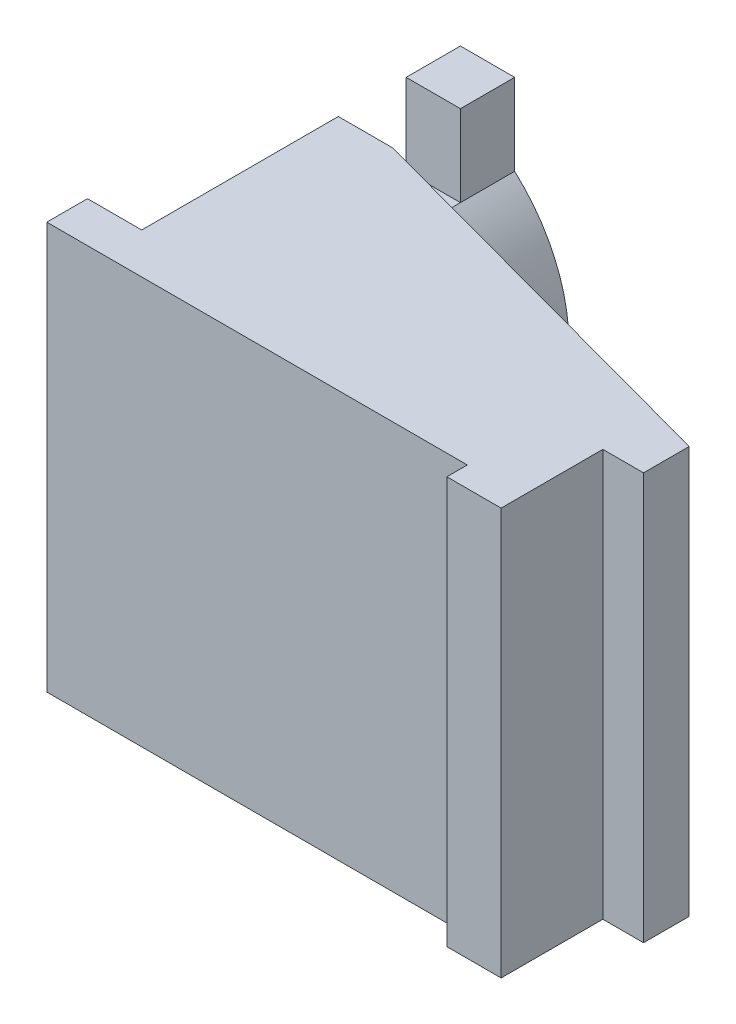
SolidWorks part; units mm, degrees
ref_plane "Front Plane" through (0, 0, 0) normal (0, 0, 1) x (1, 0, 0)
ref_plane "Top Plane" through (0, 0, 0) normal (0, 1, 0) x (1, 0, 0)
ref_plane "Right Plane" through (0, 0, 0) normal (1, 0, 0) x (0, 0, -1)
sketch "Sketch1" plane through (0, 0, 0) normal (0, 1, 0) x (1, 0, 0)
  line L4 (2, 1.5) -> (2, 13.2456)
  line L5 (2, 13.2456) -> (4, 13.2456)
  line L6 (4, 13.2456) -> (4, 8.7456)
  line L8 (17.5, -0.7544) -> (17.5, 1.1282)
  line L10 (17.5, -0.7544) -> (15.5, -0.7544)
  line L15 (17.5, 2.9956) -> (17.5, 1.1282)
  line L16 (15.5, -0.7544) -> (15.5, 0)
  line L19 (19, 4.6792) -> (19, 2.9956)
  line L20 (19, 2.9956) -> (17.5, 2.9956)
  line L21 (19, 4.6792) -> (4, 8.7456)
  line L22 (18.3909, 2.7956) -> (17.5609, 2.7956) construction
  line L23 (18.3909, 2.7456) -> (22.5609, 2.7456) construction
  line L24 (18.3909, 2.7956) -> (17.5609, 2.7956) construction
  line L25 (18.3909, 2.7456) -> (22.5609, 2.7456) construction
  line L26 (15.5, 0) -> (0, 0)
  line L28 (0, 0) -> (0, 1.5)
  line L29 (0, 1.5) -> (2, 1.5)
  line L30 (0, 13.2456) -> (2, 13.2456) construction
  line L31 (15.1609, -2.7544) -> (17.0609, -2.7544) construction
  line L32 (15.1609, -2.7544) -> (17.0609, -2.7544) construction
  dimension "D3" = 2
  dimension "D7" = 2
  dimension "D14" = 15.5
  dimension "D15" = 0.2
  dimension "D17" = 1.5
  dimension "D5" = 2
  dimension "D6" = 1.5
  dimension "D4" = 2
  dimension "D8" = 3.75
  dimension "D2" = 4.5
extrude "Boss-Extrude1" add sketch "Sketch1" along normal mid plane 15
sketch "Sketch2" plane through (0, 0, 0) normal (1, 0, 0) x (0, 0, -1)
  line L0 (13.2456, -7.5) -> (8.7456, -7.5) construction
  line L1 (13.2456, 7.5) -> (13.2456, -7.5) construction
  line L2 (13.2456, 7.5) -> (8.7456, 7.5) construction
  line L3 (13.2456, -7.5) -> (8.7456, -7.5) construction
  line L4 (13.2456, 7.5) -> (13.2456, -7.5) construction
  line L5 (13.2456, 7.5) -> (8.7456, 7.5) construction
  line L6 (0, 0) -> (50000, 0) construction
  line L7 (11.2456, 7.5) -> (11.2456, 4.5)
  line L8 (8.7456, -7.5) -> (11.2456, -7.5)
  line L9 (8.7456, -7.5) -> (8.7456, -4.5)
  line L10 (8.7456, -4.5) -> (11.2456, -4.5)
  line L11 (11.2456, -7.5) -> (11.2456, -4.5)
  line L12 (8.7456, 4.5) -> (11.2456, 4.5)
  line L13 (8.7456, 7.5) -> (8.7456, 4.5)
  line L14 (8.7456, 7.5) -> (11.2456, 7.5)
  dimension "D1" = 2
  dimension "D2" = 2.5
  dimension "D3" = 3
extrude "Cut-Extrude2" cut sketch "Sketch2" along normal through all
sketch "Sketch4" plane through (0, 0, -13.2456) normal (0, 0, -1) x (-1, 0, 0)
  line L0 (0, 0) -> (50000, 0) construction
  line L2 (-2, 7.5) -> (-2, -7.5) construction
  line L3 (-4, 4.5) -> (-2, 4.5) construction
  line L5 (-4, 4.5) -> (-4, 7.5)
  line L6 (-2, 7.5) -> (-4, 7.5) construction
  line L7 (-4, 7.5) -> (-2, 7.5)
  line L8 (-19, 7.5) -> (-4, 7.5) construction
  line L10 (-4, -7.5) -> (-2, -7.5)
  line L11 (-4, -4.5) -> (-4, -7.5)
  line L14 (-4, 4.5) -> (-4, -4.5)
  arc A0 (-4, 4.5) -> (-4, -4.5) centre (0.0625, 0) ccw
  line M6 (-4, 7.5) -> (-4, -7.5)
  dimension "D2" = 2
extrude "Boss-Extrude2" add sketch "Sketch4" against normal up to surface (4.5 mm away) contours A0 L0 M6 | L0 A0 L14
equation "\"D2@Sketch1\"=2+2.5"
